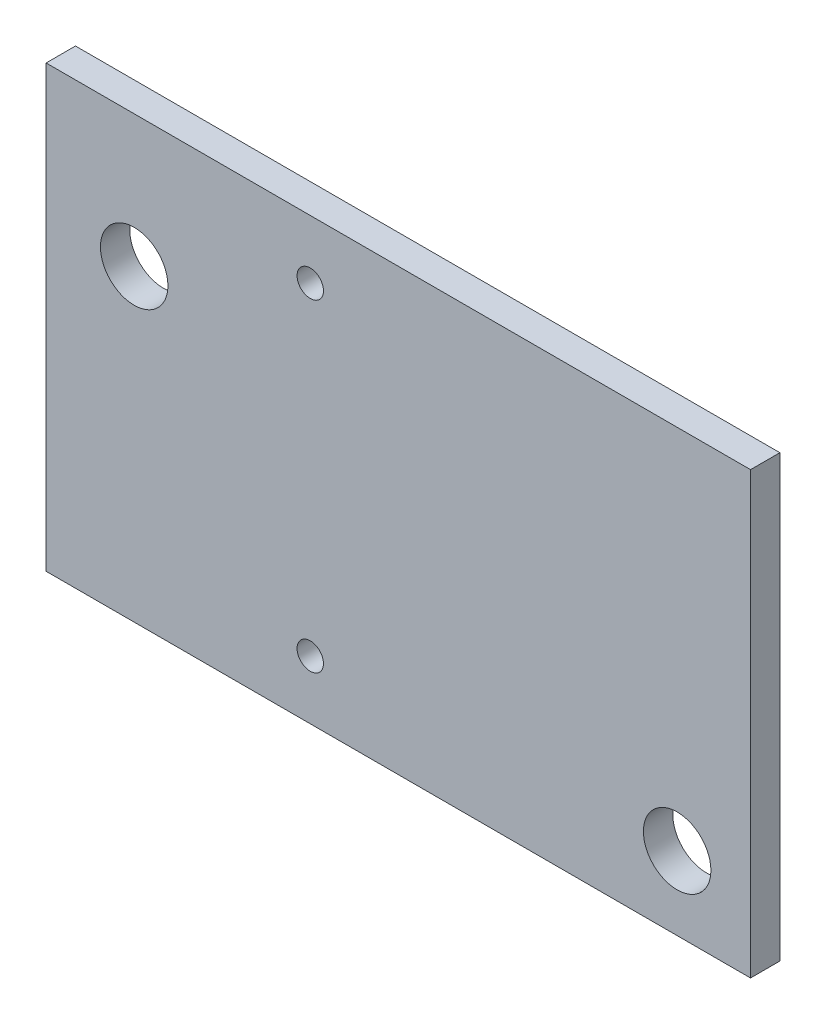
SolidWorks part; units mm, degrees
ref_plane "Спереди" through (0, 0, 0) normal (0, 0, 1) x (1, 0, 0)
ref_plane "Сверху" through (0, 0, 0) normal (0, 1, 0) x (1, 0, 0)
ref_plane "Справа" through (0, 0, 0) normal (1, 0, 0) x (0, 0, -1)
sketch "Эскиз1" plane through (0, 0, 0) normal (0, 0, 1) x (1, 0, 0)
  line L1 (0, 0) -> (24, 0)
  line L2 (0, 0) -> (0, 15)
  line L3 (0, 15) -> (24, 15)
  line L4 (24, 0) -> (24, 15)
  circle A0 centre (3, 10.5) radius 1.15
  circle A1 centre (21.5, 2.5) radius 1.15
  circle A2 centre (9, 13) radius 0.45
  circle A3 centre (9, 2) radius 0.45
  dimension "D3" = 4.5
  dimension "D5" = 8
  dimension "D6" = 18.5
  dimension "D7" = 2.3
  dimension "D11" = 0.9
  dimension "D1" = 24
  dimension "D2" = 15
  dimension "D4" = 3
  dimension "D8" = 9
  dimension "D9" = 11
  dimension "D10" = 2
extrude "Бобышка-Вытянуть1" add sketch "Эскиз1" along normal blind 1
